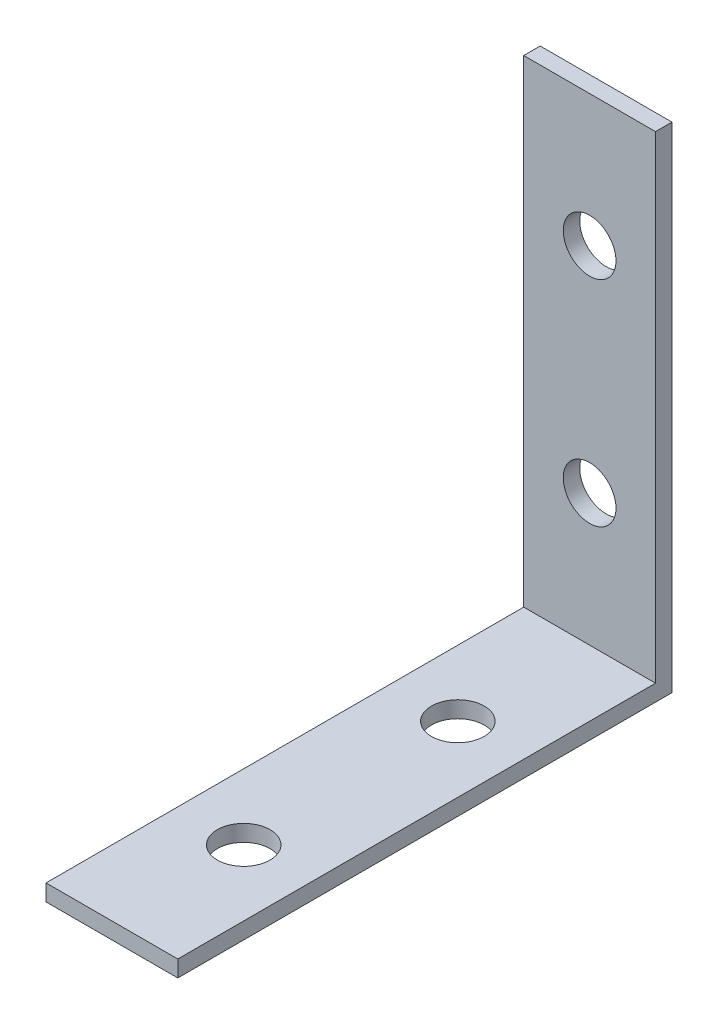
SolidWorks part; units mm, degrees
ref_plane "Front Plane" through (0, 0, 0) normal (0, 0, 1) x (1, 0, 0)
ref_plane "Top Plane" through (0, 0, 0) normal (0, 1, 0) x (1, 0, 0)
ref_plane "Right Plane" through (0, 0, 0) normal (1, 0, 0) x (0, 0, -1)
sketch "Sketch1" plane through (0, 0, 0) normal (0, 1, 0) x (1, 0, 0)
  line L1 (-10, 37.5) -> (10, 37.5)
  line L2 (-10, 37.5) -> (-10, -37.5)
  line L3 (-10, -37.5) -> (10, -37.5)
  line L4 (10, 37.5) -> (10, -37.5)
  line L5 (-10, 37.5) -> (10, -37.5) construction
  line L6 (-10, -37.5) -> (10, 37.5) construction
  point P0 (0, 0)
  dimension "D1" = 20
  dimension "D2" = 75
extrude "Boss-Extrude1" add sketch "Sketch1" along normal blind 2.5
sketch "Sketch2" plane through (0, 2.5, 0) normal (0, 1, 0) x (1, 0, 0)
  line L0 (10, -37.5) -> (10, 37.5) construction
  line L1 (-10, 37.5) -> (10, 37.5)
  line L2 (-10, 37.5) -> (-10, 35)
  line L3 (-10, 35) -> (10, 35)
  line L4 (10, 37.5) -> (10, 35)
  dimension "D1" = 2.5
extrude "Boss-Extrude2" add sketch "Sketch2" along normal blind 72.5
sketch "Sketch3" plane through (0, 2.5, 0) normal (0, 1, 0) x (1, 0, 0)
  line L0 (0, 35) -> (0, -37.5) construction
  line L1 (-10, 35) -> (10, 35) construction
  line L2 (-10, -37.5) -> (10, -37.5) construction
  circle A0 centre (0, 15) radius 4
  circle A1 centre (0, -17.5) radius 4
  dimension "D1" = 8
  dimension "D2" = 8
  dimension "D3" = 20
  dimension "D4" = 20
extrude "Cut-Extrude1" cut sketch "Sketch3" against normal blind 2.5
sketch "Sketch4" plane through (0, 0, -35) normal (0, 0, 1) x (1, 0, 0)
  line L0 (0, 75) -> (0, 0) construction
  line L1 (-10, 75) -> (10, 75) construction
  line L2 (-10, 2.5) -> (10, 2.5) construction
  circle A0 centre (0, 55) radius 4
  circle A1 centre (0, 22.5) radius 4
  dimension "D1" = 8
  dimension "D2" = 8
  dimension "D3" = 20
  dimension "D4" = 20
extrude "Cut-Extrude2" cut sketch "Sketch4" against normal blind 2.5
